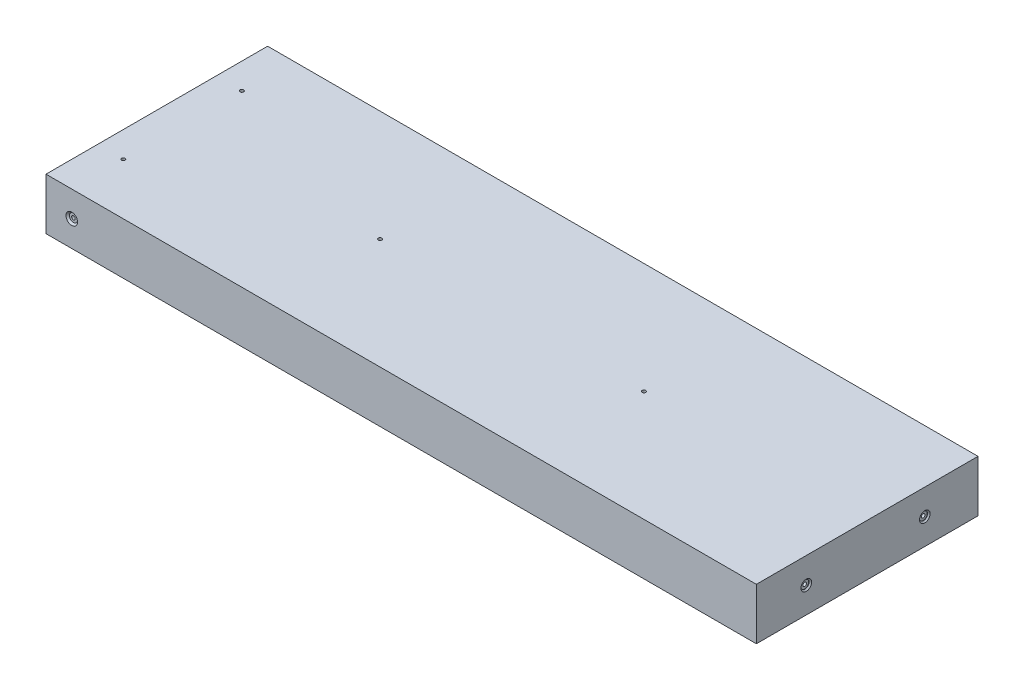
SolidWorks part; units mm, degrees
ref_plane "Front Plane" through (0, 0, 0) normal (0, 0, 1) x (1, 0, 0)
ref_plane "Top Plane" through (0, 0, 0) normal (0, 1, 0) x (1, 0, 0)
ref_plane "Right Plane" through (0, 0, 0) normal (1, 0, 0) x (0, 0, -1)
sketch "Sketch1" plane through (0, 0, 0) normal (0, 1, 0) x (1, 0, 0)
  line L1 (-175, 54.6) -> (175, 54.6)
  line L2 (-175, 54.6) -> (-175, -54.6)
  line L3 (-175, -54.6) -> (175, -54.6)
  line L4 (175, 54.6) -> (175, -54.6)
  line L5 (-175, 54.6) -> (175, -54.6) construction
  line L6 (-175, -54.6) -> (175, 54.6) construction
  point P0 (0, 0)
  dimension "D1" = 109.2
  dimension "D2" = 350
extrude "Boss-Extrude1" add sketch "Sketch1" along normal blind 25.4
hole_wizard "CBORE for #0 Binding Head Machine Screw1" positions "Sketch2" profile "Sketch3" counterbore size "#0" standard "ANSI Inch"
sketch "Sketch2" plane through (0, 0, 54.6) normal (0, 0, 1) x (1, 0, 0)
  line L0 (-175, 25.4) -> (-175, 0) construction
  line L1 (-175, 25.4) -> (175, 25.4) construction
  point P0 (-162.3, 12.7)
  dimension "D1" = 12.7
  dimension "D2" = 12.7
sketch "Sketch3" plane through (-162.3, 12.7, 54.6) normal (1, 0, 0) x (0, -1, 0)
  line L0 (0, 0) -> (0, 30.5342)
  line L1 (0, 30.5342) -> (0.889, 30)
  line L2 (0.889, 30) -> (0.889, 0.8128)
  line L3 (0.889, 0.8128) -> (1.985, 0.8128)
  line L5 (1.985, 0.8128) -> (1.985, 0.8725)
  line L6 (1.985, 0.8725) -> (2.8575, 0)
  line L7 (2.8575, 0) -> (0, 0)
  line L8 (-1.985, 0.8725) -> (-2.8575, 0) construction
  line L10 (0, 30.5342) -> (-0.889, 30) construction
  line L11 (0, -6.35) -> (0, 107.95) construction
  dimension "Hole Dia." = 1.778
  dimension "Hole Depth" = 30
  dimension "C'Bore Dia." = 3.97
  dimension "C'Bore Depth" = 0.8128
  dimension "Near C'Sink Dia." = 5.715
  dimension "Near C'Sink Angle" = 90
  dimension "Drill Angle" = 118
mirror "Mirror1" about plane through (0, 0, 0) normal (0, 0, 1) of "CBORE for #0 Binding Head Machine Screw1"
hole_wizard "CBORE for #0 Binding Head Machine Screw2" positions "Sketch4" profile "Sketch5" counterbore size "#0" standard "ANSI Inch"
sketch "Sketch4" plane through (175, 0, 0) normal (1, 0, 0) x (0, 0, -1)
  line L0 (-54.6, 25.4) -> (-54.6, 0) construction
  line L2 (-54.6, 25.4) -> (54.6, 25.4) construction
  point P0 (-30, 12.7)
  point P2 (28.4, 12.7)
  dimension "D1" = 58.4
  dimension "D2" = 24.6
  dimension "D4" = 12.7
sketch "Sketch5" plane through (175, 12.7, 30) normal (0, 1, 0) x (0, 0, -1)
  line L0 (0, 0) -> (0, 30.5342)
  line L1 (0, 30.5342) -> (0.889, 30)
  line L2 (0.889, 30) -> (0.889, 0.8128)
  line L3 (0.889, 0.8128) -> (1.985, 0.8128)
  line L5 (1.985, 0.8128) -> (1.985, 0.635)
  line L6 (1.985, 0.635) -> (2.62, 0)
  line L7 (2.62, 0) -> (0, 0)
  line L8 (-1.985, 0.635) -> (-2.62, 0) construction
  line L10 (0, 30.5342) -> (-0.889, 30) construction
  line L11 (0, -6.35) -> (0, 107.95) construction
  dimension "Hole Dia." = 1.778
  dimension "Hole Depth" = 30
  dimension "C'Bore Dia." = 3.97
  dimension "C'Bore Depth" = 0.8128
  dimension "Near C'Sink Dia." = 5.24
  dimension "Near C'Sink Angle" = 90
  dimension "Drill Angle" = 118
hole_wizard "CBORE for #0 Binding Head Machine Screw4" positions "Sketch8" profile "Sketch9" counterbore size "#0" standard "ANSI Inch"
sketch "Sketch8" plane through (0, 0, 0) normal (0, -1, 0) x (-1, 0, 0)
  line L0 (0, 54.6) -> (0, -54.6) construction
  line L1 (-175, 54.6) -> (175, 54.6) construction
  line L2 (175, -54.6) -> (-175, -54.6) construction
  line L4 (175, 0) -> (-175, 0) construction
  line L5 (175, 54.6) -> (175, -54.6) construction
  line L6 (-175, -54.6) -> (-175, 54.6) construction
  point P0 (65, 0)
  point P2 (-65, 0)
  dimension "D1" = 130
sketch "Sketch9" plane through (-65, 0, 0) normal (1, 0, 0) x (0, 0, -1)
  line L0 (0, 0) -> (0, 30.5342)
  line L1 (0, 30.5342) -> (0.889, 30)
  line L2 (0.889, 30) -> (0.889, 0.8128)
  line L3 (0.889, 0.8128) -> (1.985, 0.8128)
  line L5 (1.985, 0.8128) -> (1.985, 0.8725)
  line L6 (1.985, 0.8725) -> (2.8575, 0)
  line L7 (2.8575, 0) -> (0, 0)
  line L8 (-1.985, 0.8725) -> (-2.8575, 0) construction
  line L10 (0, 30.5342) -> (-0.889, 30) construction
  line L11 (0, -6.35) -> (0, 107.95) construction
  dimension "Hole Dia." = 1.778
  dimension "Hole Depth" = 30
  dimension "C'Bore Dia." = 3.97
  dimension "C'Bore Depth" = 0.8128
  dimension "Near C'Sink Dia." = 5.715
  dimension "Near C'Sink Angle" = 90
  dimension "Drill Angle" = 118
hole_wizard "CBORE for #0 Binding Head Machine Screw6" positions "Sketch12" profile "Sketch13" counterbore size "#0" standard "ANSI Inch" end condition through all
sketch "Sketch12" plane through (0, 0, 0) normal (0, -1, 0) x (-1, 0, 0)
  line L0 (175, 54.6) -> (175, -54.6) construction
  line L1 (-175, 54.6) -> (175, 54.6) construction
  point P0 (162.3, 29.2)
  point P2 (162.3, -29.2)
  dimension "D1" = 12.7
  dimension "D2" = 12.7
  dimension "D3" = 58.4
  dimension "D4" = 25.4
sketch "Sketch13" plane through (-162.3, 0, -29.2) normal (1, 0, 0) x (0, 0, -1)
  line L0 (0, 0) -> (0, 25.4)
  line L1 (0, 25.4) -> (0.889, 25.4)
  line L3 (0.889, 25.4) -> (0.889, 0.8128)
  line L4 (1.985, 0.8128) -> (0.889, 0.8128)
  line L5 (1.985, 0.8128) -> (1.985, 0.8725)
  line L6 (1.985, 0.8725) -> (2.8575, 0)
  line L7 (2.8575, 0) -> (0, 0)
  line L8 (-1.985, 0.8725) -> (-2.8575, 0) construction
  line L11 (0, -6.35) -> (0, 107.95) construction
  dimension "Thru Hole Dia." = 1.778
  dimension "Thru Hole Depth" = 25.4
  dimension "C'Bore Dia." = 3.97
  dimension "C'Bore Depth" = 0.8128
  dimension "Near C'Sink Dia." = 5.715
  dimension "Near C'Sink Angle" = 90
